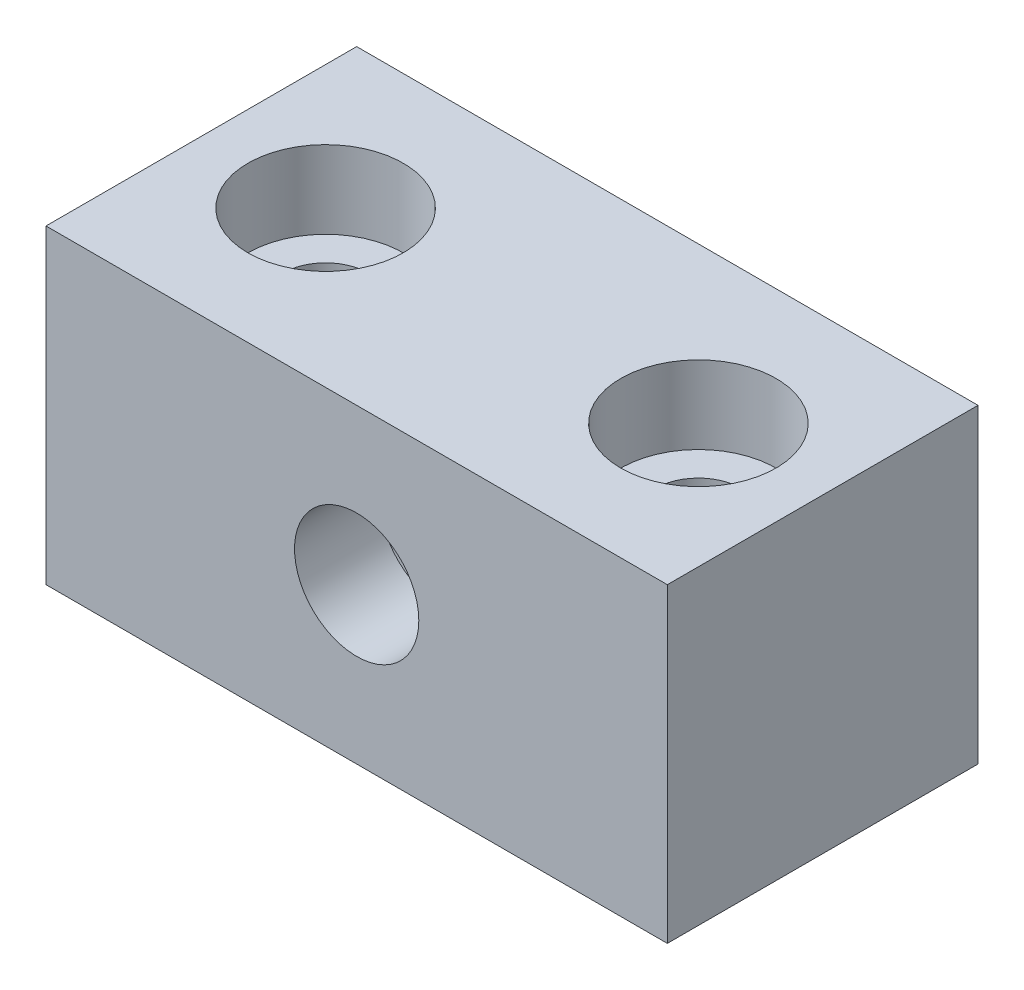
SolidWorks part; units mm, degrees
ref_plane "Front Plane" through (0, 0, 0) normal (0, 0, 1) x (1, 0, 0)
ref_plane "Top Plane" through (0, 0, 0) normal (0, 1, 0) x (1, 0, 0)
ref_plane "Right Plane" through (0, 0, 0) normal (1, 0, 0) x (0, 0, -1)
sketch "Sketch1" plane through (0, 0, 0) normal (0, 0, 1) x (1, 0, 0)
  line L1 (0, 0) -> (40, 0)
  line L2 (0, 0) -> (0, 20)
  line L3 (0, 20) -> (40, 20)
  line L4 (40, 0) -> (40, 20)
  dimension "D1" = 20
  dimension "D2" = 40
extrude "Boss-Extrude1" add sketch "Sketch1" along normal blind 20
sketch "Sketch2" plane through (0, 20, 0) normal (0, 1, 0) x (1, 0, 0)
  line L0 (0, -20) -> (0, 0) construction
  circle A0 centre (8, -10) radius 2.75
  circle A1 centre (32, -10) radius 2.75
  point P6 (0, -10)
  dimension "D3" = 5.5
  dimension "D4" = 5.5
  dimension "D1" = 8
  dimension "D2" = 24
extrude "Cut-Extrude1" cut sketch "Sketch2" against normal through all
sketch "Sketch3" plane through (0, 20, 0) normal (0, 1, 0) x (1, 0, 0)
  circle A0 centre (8, -10) radius 5
  circle A1 centre (32, -10) radius 5
  dimension "D1" = 10
  dimension "D2" = 10
extrude "Cut-Extrude2" cut sketch "Sketch3" against normal blind 5
sketch "Sketch4" plane through (0, 0, 20) normal (0, 0, 1) x (1, 0, 0)
  circle A0 centre (20, 10) radius 4
  dimension "D1" = 8
extrude "Cut-Extrude3" cut sketch "Sketch4" against normal blind 5.5
sketch "Sketch5" plane through (0, 0, 0) normal (0, 0, -1) x (-1, 0, 0)
  circle A0 centre (-20, 10) radius 4
  dimension "D1" = 8
extrude "Cut-Extrude4" cut sketch "Sketch5" against normal blind 5.5
sketch "Sketch6" plane through (0, 0, 14.5) normal (0, 0, 1) x (1, 0, 0)
  circle A0 centre (20, 10) radius 3.5
  dimension "D1" = 7
extrude "Cut-Extrude5" cut sketch "Sketch6" against normal through all
